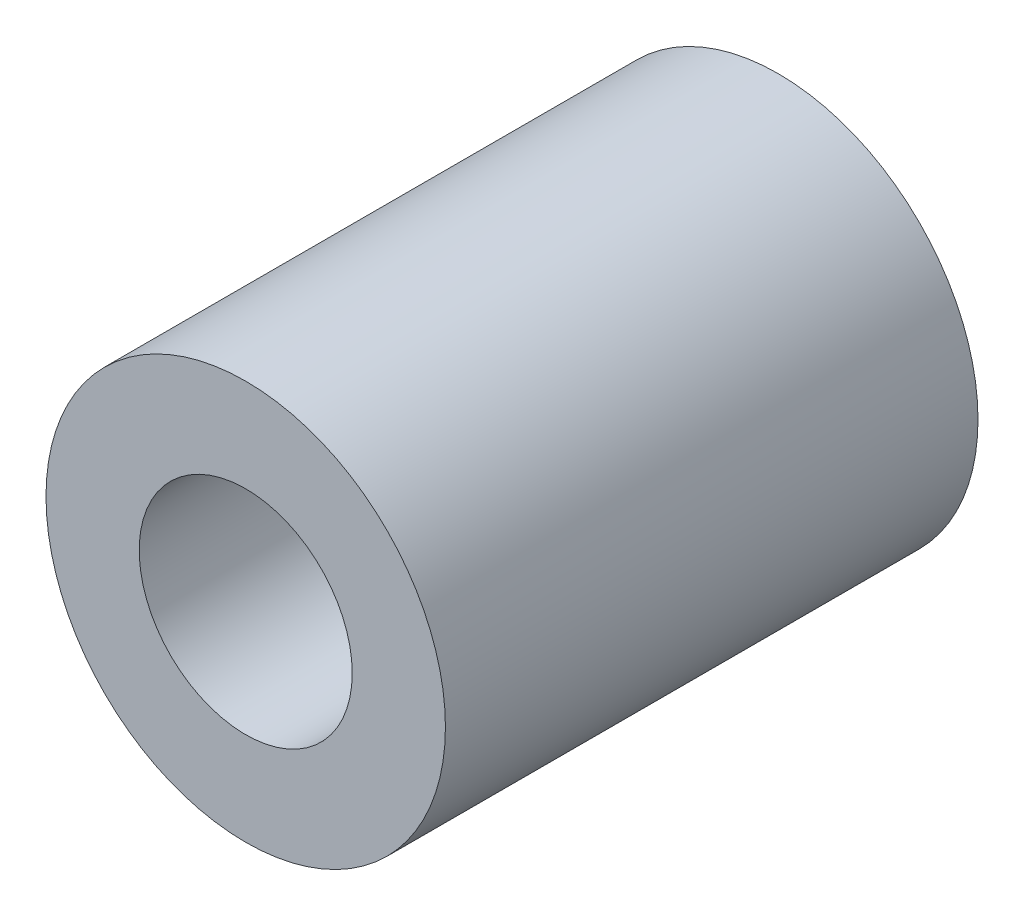
SolidWorks part; units mm, degrees
material "Plain Carbon Steel"
ref_plane "Front Plane" through (0, 0, 0) normal (0, 0, 1) x (1, 0, 0)
ref_plane "Top Plane" through (0, 0, 0) normal (0, 1, 0) x (1, 0, 0)
ref_plane "Right Plane" through (0, 0, 0) normal (1, 0, 0) x (0, 0, -1)
sketch "Sketch1" plane through (0, 0, 0) normal (0, 0, 1) x (1, 0, 0)
  circle A0 centre (0, 0) radius 1.6
  circle A1 centre (0, 0) radius 3
  dimension "D1" = 6
  dimension "D2" = 3.2
extrude "Boss-Extrude1" add sketch "Sketch1" along normal blind 8
